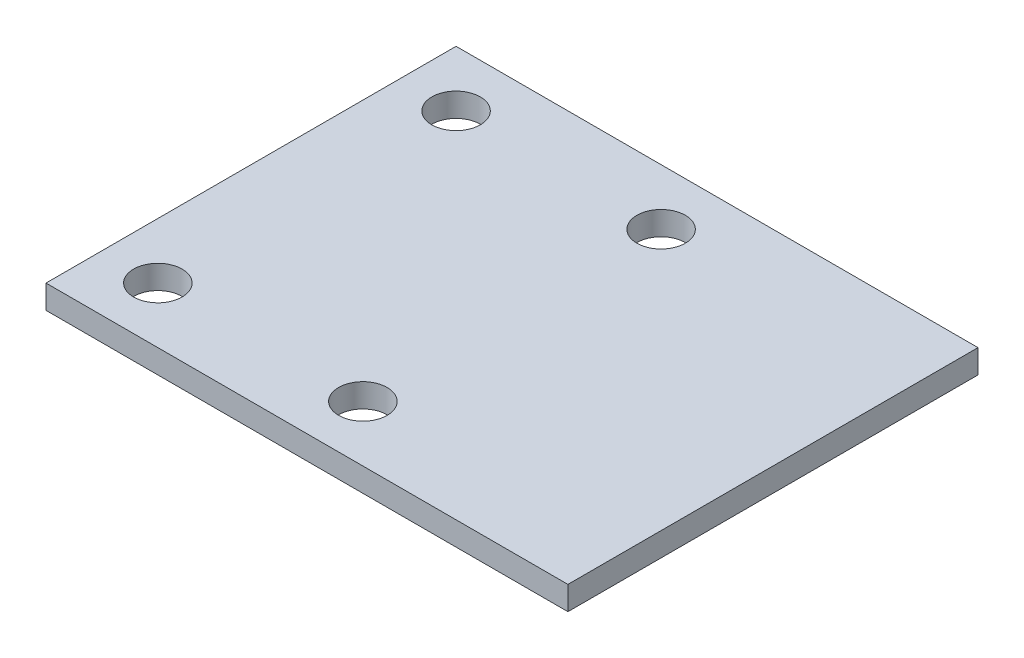
SolidWorks part; units mm, degrees
material "Copper"
ref_plane "Front Plane" through (0, 0, 0) normal (0, 0, 1) x (1, 0, 0)
ref_plane "Top Plane" through (0, 0, 0) normal (0, 1, 0) x (1, 0, 0)
ref_plane "Right Plane" through (0, 0, 0) normal (1, 0, 0) x (0, 0, -1)
sketch "Sketch1" plane through (0, 0, 0) normal (0, 1, 0) x (1, 0, 0)
  line L0 (14, 11) -> (-14, -11) construction
  line L1 (-14, 11) -> (14, 11)
  line L2 (-14, 11) -> (-14, -11)
  line L3 (-14, -11) -> (14, -11)
  line L4 (14, 11) -> (14, -11)
  point P4 (0, 0)
  dimension "D1" = 28
  dimension "D2" = 22
extrude "Boss-Extrude1" add sketch "Sketch1" along normal blind 1.27
sketch "Sketch2" plane through (0, 0, 0) normal (0, 1, 0) x (1, 0, 0)
  line L1 (14, 11) -> (-14, 11) construction
  line L2 (-14, 11) -> (-14, -11) construction
  circle A0 centre (-11, 8) radius 1.3
  dimension "D1" = 2.6
  dimension "D2" = 3
  dimension "D3" = 3
extrude "Cut-Extrude2" cut sketch "Sketch2" along normal through all
pattern_linear "LPattern1" count 2 spacing 11 along (1, 0, 0) count 2 spacing 16 along (0, 0, 1) of "Cut-Extrude2"
